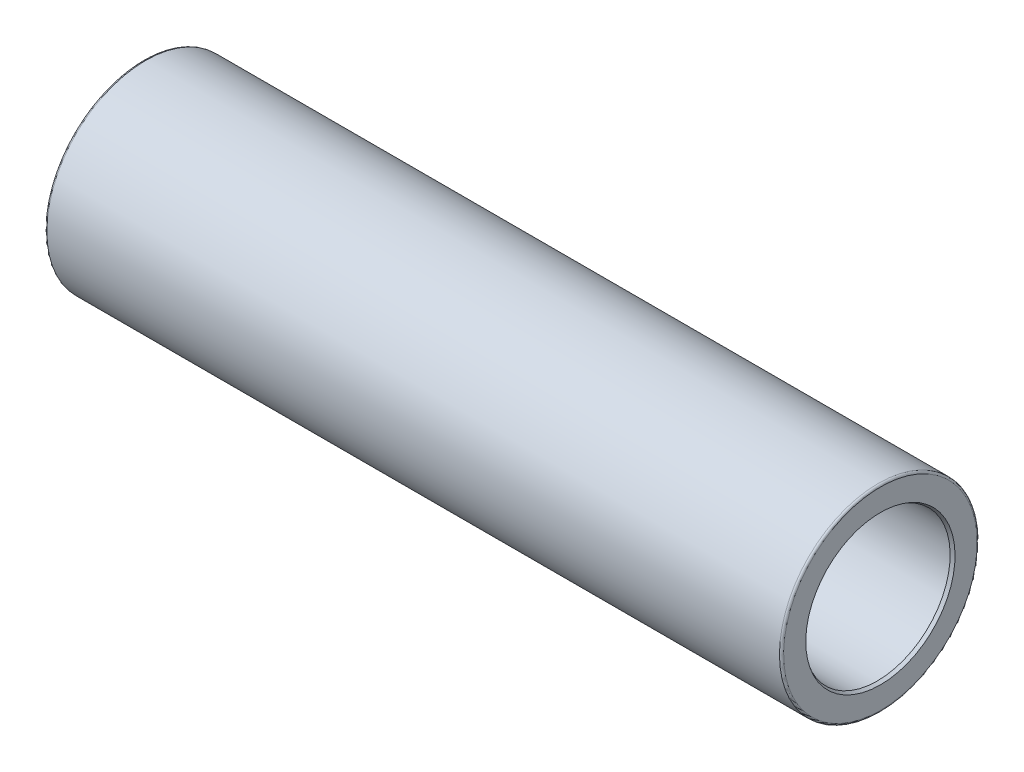
SolidWorks part; units mm, degrees
ref_plane "Plane1" through (0, 0, 0) normal (0, 0, 1) x (1, 0, 0)
ref_plane "Plane2" through (0, 0, 0) normal (0, 1, 0) x (1, 0, 0)
ref_plane "Plane3" through (0, 0, 0) normal (1, 0, 0) x (0, 0, -1)
sketch "Sketch1" plane through (0, 0, 0) normal (0, 0, 1) x (1, 0, 0)
  line L0 (-177, 0) -> (177, 0) construction
  line L1 (0, 93.3) -> (0, -101.2) construction
  line L2 (-177, 35) -> (-177, 46.5)
  line L3 (-176, 47.5) -> (176, 47.5)
  line L5 (-177, 35) -> (-110.9626, 35)
  line L6 (-110.9626, 35) -> (-109, 36)
  line L7 (-109, 36) -> (-107, 36)
  line L8 (-107, 36) -> (-107, 34)
  line L9 (-107, 34) -> (-97.1763, 34)
  line L10 (107, 36) -> (107, 34)
  line L11 (109, 36) -> (107, 36)
  line L12 (110.9626, 35) -> (109, 36)
  line L13 (177, 35) -> (110.9626, 35)
  line L15 (177, 35) -> (177, 46.5)
  line L16 (-96.8343, 34.0603) -> (-87.5495, 37.4397)
  line L17 (-87.2075, 37.5) -> (87.2075, 37.5)
  line L18 (96.8343, 34.0603) -> (87.5495, 37.4397)
  line L19 (97.1763, 34) -> (107, 34)
  arc A0 (-87.2075, 37.5) -> (-87.5495, 37.4397) centre (-87.2075, 36.5) ccw
  arc A1 (-97.1763, 34) -> (-96.8343, 34.0603) centre (-97.1763, 35) ccw
  arc A2 (87.2075, 37.5) -> (87.5495, 37.4397) centre (87.2075, 36.5) cw
  arc A3 (97.1763, 34) -> (96.8343, 34.0603) centre (97.1763, 35) cw
  arc A4 (-176, 47.5) -> (-177, 46.5) centre (-176, 46.5) ccw
  arc A5 (176, 47.5) -> (177, 46.5) centre (176, 46.5) cw
  point P23 (0, 47.5)
  point P26 (0, 37.5)
  point P28 (-87.3838, 37.5)
  point P31 (-97, 34)
  point P34 (87.3838, 37.5)
  point P37 (97, 34)
  point P40 (-177, 47.5)
  point P43 (177, 47.5)
  dimension "D14" = 1
  dimension "D15" = 1
  dimension "D1" = 354
  dimension "D2" = 95
  dimension "D4" = 27
  dimension "D5" = 70
  dimension "D6" = 70
  dimension "D7" = 75
  dimension "D9" = 2
  dimension "D10" = 72
  dimension "D11" = 68
  dimension "D12" = 20
  dimension "D13" = 80
revolve "Base-Revolve" add sketch "Sketch1" angle 360 about L0
sketch "Sketch5" plane through (0, 0, 0) normal (0, 0, 1) x (1, 0, 0)
  line L0 (0, 0) -> (177, 0) construction
  line L1 (177, -46.5) -> (177, 46.5) construction
  line L2 (0, 0) -> (0, 47.5) construction
  line L3 (176, 47.5) -> (-176, 47.5) construction
  line L4 (177, 35) -> (110.9626, 35) construction
  line L5 (-177, 35) -> (-177, 35.866)
  line L6 (177, 35) -> (175.5, 35)
  line L7 (175.5, 35) -> (177, 35.866)
  line L8 (177, 35) -> (177, 35.866)
  line L9 (-175.5, 35) -> (-177, 35.866)
  line L10 (-177, 35) -> (-175.5, 35)
  dimension "D1" = 30
  dimension "D2" = 1.5
revolve "Reifning 2.5 x 30 gr" cut sketch "Sketch5" angle 360 about L0
sketch "Sketch4" plane through (0, 0, 0) normal (1, 0, 0) x (0, 0, -1)
  line L1 (0, 0) -> (47.5, 0) construction
  line L2 (47.5, 0) -> (47.5, 10)
  line L3 (47.5, 10) -> (45.5, 10)
  line L4 (45.5, 10) -> (42.1352, 4.4)
  line L5 (42.1352, 4.4) -> (17.5, 4.4)
  line L6 (17.5, 4.4) -> (17.5, 0)
  line L7 (47.5, 0) -> (17.5, 0)
  line L8 (0, 0) -> (0, 47.5) construction
  circle A1 centre (0, 0) radius 47.5 construction
  circle A2 centre (0, 0) radius 47.5 construction
  dimension "D1" = 90
  dimension "D2" = 20
  dimension "D3" = 8.8
  dimension "D4" = 59
  dimension "D5" = 2
  dimension "D6" = 30
revolve "Udboring smørenippel" [suppressed] cut sketch "Sketch4" angle 360 about L1
cosmetic thread "Cosmetic Thread1" [suppressed] parameters "D2"=9.728
